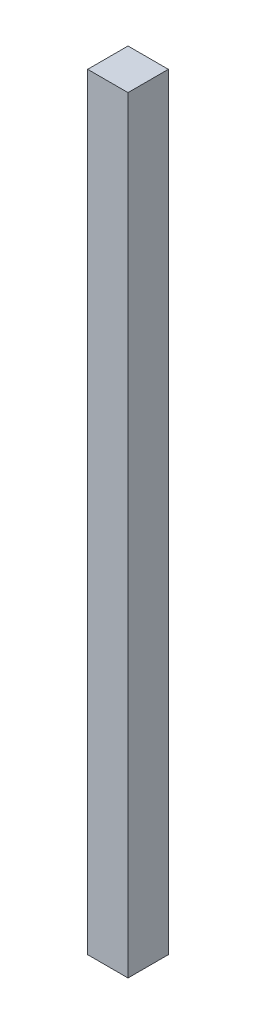
SolidWorks part; units mm, degrees
ref_plane "Front Plane" through (0, 0, 0) normal (0, 0, 1) x (1, 0, 0)
ref_plane "Top Plane" through (0, 0, 0) normal (0, 1, 0) x (1, 0, 0)
ref_plane "Right Plane" through (0, 0, 0) normal (1, 0, 0) x (0, 0, -1)
sketch "Sketch1" plane through (0, 0, 0) normal (0, 1, 0) x (1, 0, 0)
  line L1 (1.5, 1.5) -> (-1.5, 1.5)
  line L2 (1.5, 1.5) -> (1.5, -1.5)
  line L3 (1.5, -1.5) -> (-1.5, -1.5)
  line L4 (-1.5, 1.5) -> (-1.5, -1.5)
  line L5 (1.5, 1.5) -> (-1.5, -1.5) construction
  line L6 (1.5, -1.5) -> (-1.5, 1.5) construction
  dimension "D1" = 3
extrude "Boss-Extrude1" add sketch "Sketch1" along normal blind 57
scale "Scale1" scale about centroid uniform scaling yes scale factor 10
